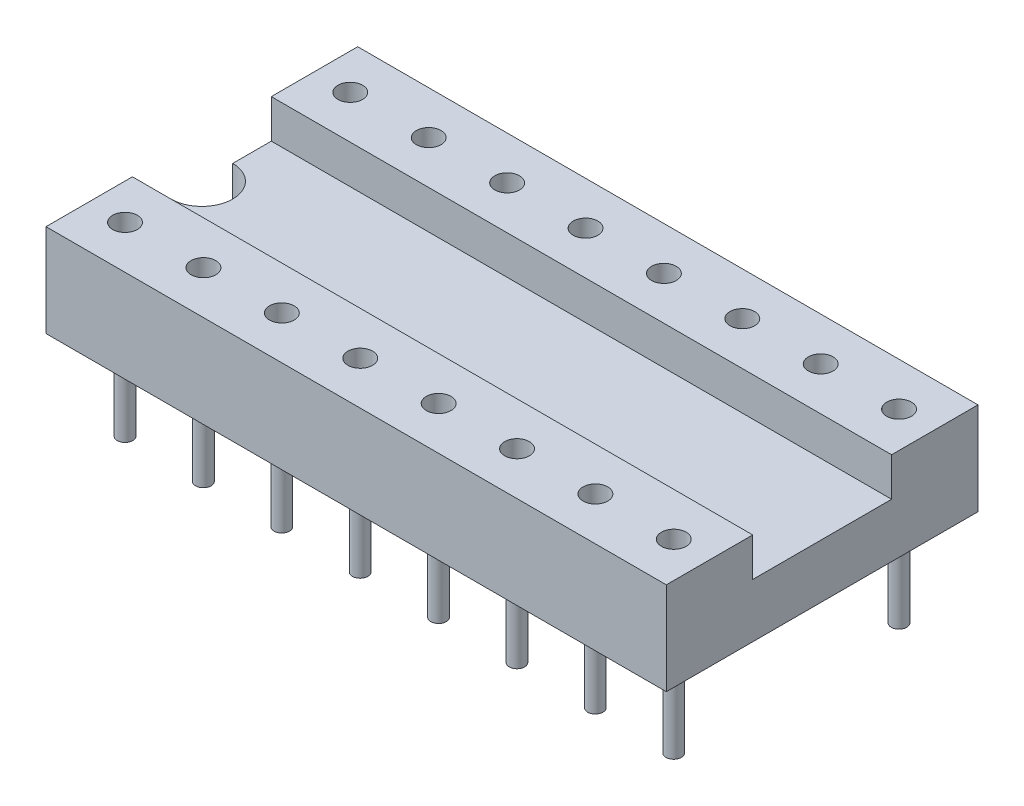
SolidWorks part; units mm, degrees
ref_plane "Plan de face" through (0, 0, 0) normal (0, 0, 1) x (1, 0, 0)
ref_plane "Plan de dessus" through (0, 0, 0) normal (0, 1, 0) x (1, 0, 0)
ref_plane "Plan de droite" through (0, 0, 0) normal (1, 0, 0) x (0, 0, -1)
sketch "Esquisse1" plane through (0, 0, 0) normal (1, 0, 0) x (0, 0, -1)
  line L0 (12.2051, 0) -> (-23.3437, 0) construction
  line L1 (0, -4.6214) -> (0, 25.9507) construction
  line L2 (-5.7968, 1.75) -> (2.763, 1.75) construction
  line L3 (5.7565, 3) -> (-6.8307, 3) construction
  line L4 (5.05, 3.8077) -> (5.05, -1.0493) construction
  line L5 (-5.05, 3.7235) -> (-5.05, -1.0493) construction
  line L6 (-2.25, 3.5071) -> (-2.25, 0.8142) construction
  line L7 (2.25, 3.5071) -> (2.25, 0.8142) construction
  line L8 (-2.25, 1.75) -> (-2.25, 3)
  line L9 (-2.25, 3) -> (-5.05, 3)
  line L10 (-5.05, 3) -> (-5.05, 0)
  line L11 (-5.05, 0) -> (5.05, 0)
  line L12 (5.05, 0) -> (5.05, 3)
  line L13 (5.05, 3) -> (2.25, 3)
  line L14 (2.25, 3) -> (2.25, 1.75)
  line L15 (2.25, 1.75) -> (-2.25, 1.75)
  dimension "D1" = 1.75
  dimension "D2" = 3
  dimension "D3" = 5.05
  dimension "D4" = 5.05
  dimension "D5" = 2.8
  dimension "D6" = 2.8
extrude "Extrusion1" add sketch "Esquisse1" along normal blind 20.1
sketch "Esquisse2" plane through (0, 1.75, 0) normal (0, 1, 0) x (-1, 0, 0)
  line L0 (0, -1) -> (0, 1)
  arc A0 (0, 1) -> (0, -1) centre (0, 0) ccw
extrude "Enlèv. mat.-Extru.1" cut sketch "Esquisse2" against normal through all
sketch "Esquisse3" plane through (0, 3, 0) normal (0, 1, 0) x (-1, 0, 0)
  line L0 (-13.1576, 5.05) -> (2.3638, 5.05) construction
  line L1 (0, 6.1465) -> (0, -6.3771) construction
  line L2 (1.5124, 0) -> (-12.9979, 0) construction
  line L3 (1.0512, 3.65) -> (-15.6055, 3.65) construction
  line L4 (-1.16, 6.2884) -> (-1.16, 1.7827) construction
  circle A0 centre (-1.16, 3.65) radius 0.4
  circle A1 centre (-1.16, -3.65) radius 0.4
  circle A2 centre (-3.701, 3.65) radius 0.4
  circle A3 centre (-3.701, -3.65) radius 0.4
  circle A4 centre (-6.242, 3.65) radius 0.4
  circle A5 centre (-6.242, -3.65) radius 0.4
  circle A6 centre (-8.783, 3.65) radius 0.4
  circle A7 centre (-8.783, -3.65) radius 0.4
  circle A8 centre (-11.323, 3.65) radius 0.4
  circle A9 centre (-11.323, -3.65) radius 0.4
  circle A10 centre (-13.863, 3.65) radius 0.4
  circle A11 centre (-13.863, -3.65) radius 0.4
  circle A12 centre (-16.403, 3.65) radius 0.4
  circle A13 centre (-16.403, -3.65) radius 0.4
  circle A14 centre (-18.943, 3.65) radius 0.4
  circle A15 centre (-18.943, -3.65) radius 0.4
  dimension "D1" = 1.4
  dimension "D2" = 1.16
extrude "Enlèv. mat.-Extru.2" cut sketch "Esquisse3" against normal blind 2.5
sketch "Esquisse5" plane through (0, 0, 0) normal (0, -1, 0) x (1, 0, 0)
  line L0 (-0.4263, 0) -> (10.6481, 0) construction
  circle A0 centre (1.16, 3.65) radius 0.25
  circle A1 centre (1.16, -3.65) radius 0.25
  circle A2 centre (3.7, -3.65) radius 0.25
  circle A3 centre (3.7, 3.65) radius 0.25
  circle A4 centre (6.24, -3.65) radius 0.25
  circle A5 centre (6.24, 3.65) radius 0.25
  circle A6 centre (8.78, -3.65) radius 0.25
  circle A7 centre (8.78, 3.65) radius 0.25
  circle A8 centre (11.32, -3.65) radius 0.25
  circle A9 centre (11.32, 3.65) radius 0.25
  circle A10 centre (13.86, -3.65) radius 0.25
  circle A11 centre (13.86, 3.65) radius 0.25
  circle A12 centre (16.4, -3.65) radius 0.25
  circle A13 centre (16.4, 3.65) radius 0.25
  circle A14 centre (18.94, -3.65) radius 0.25
  circle A15 centre (18.94, 3.65) radius 0.25
extrude "Extrusion2" add sketch "Esquisse5" along normal blind 3
